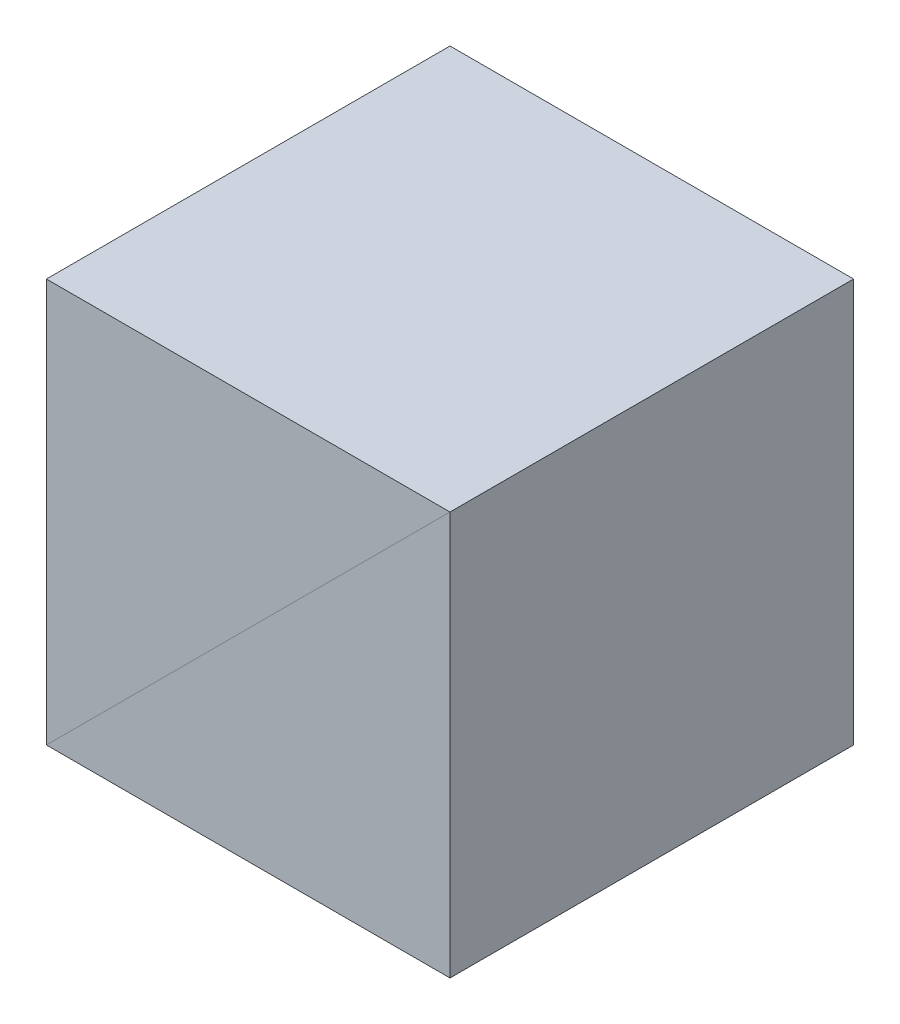
SolidWorks part; units mm, degrees
ref_plane "前视基准面" through (0, 0, 0) normal (0, 0, 1) x (1, 0, 0)
ref_plane "上视基准面" through (0, 0, 0) normal (0, 1, 0) x (1, 0, 0)
ref_plane "右视基准面" through (0, 0, 0) normal (1, 0, 0) x (0, 0, -1)
sketch "草图1" plane through (0, 0, 0) normal (0, 0, 1) x (1, 0, 0)
  line L3 (-6.35, -6.35) -> (6.35, -6.35)
  line L4 (6.35, 6.35) -> (6.35, -6.35)
  line L5 (6.35, 6.35) -> (-6.35, -6.35)
  dimension "D1" = 12.7
extrude "凸台-拉伸1" add sketch "草图1" along normal mid plane 12.7
mirror "镜向2" about plane through (6.35, 6.35, 6.35) normal (0.7071, -0.7071, 0) of bodies 107
